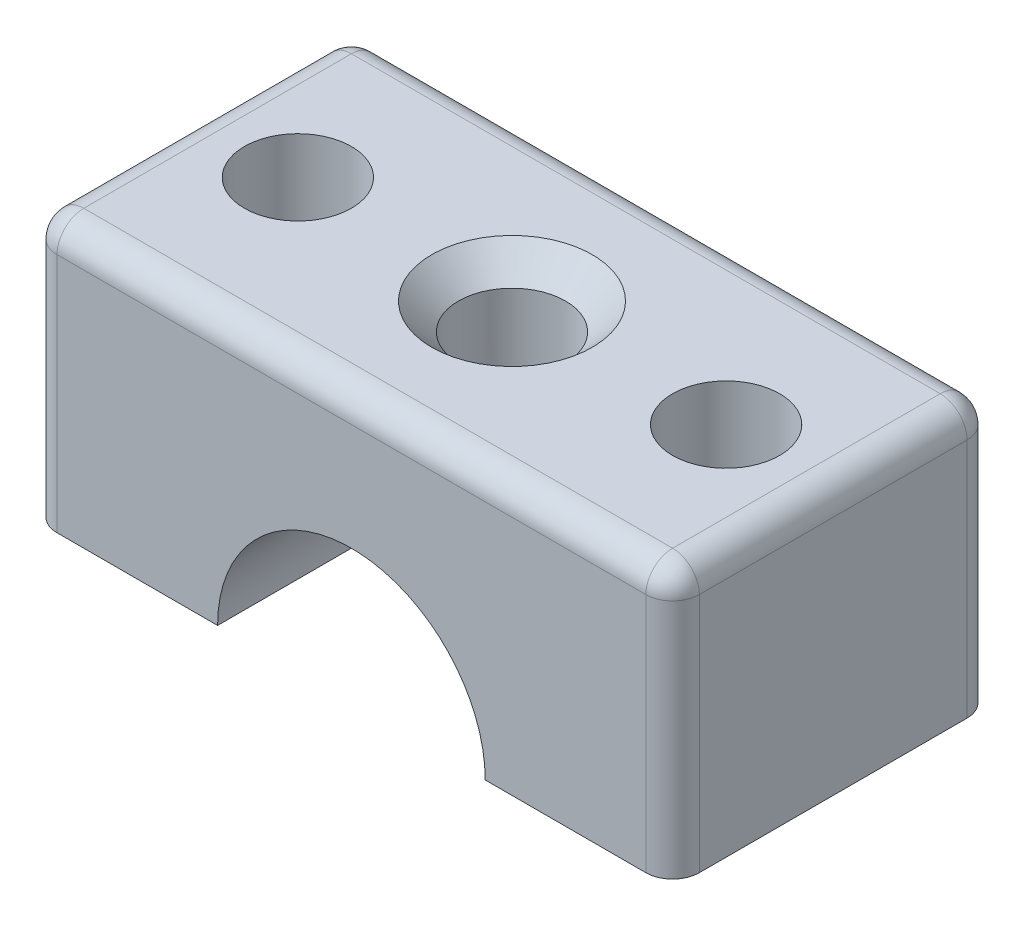
SolidWorks part; units mm, degrees
ref_plane "Front Plane" through (0, 0, 0) normal (0, 0, 1) x (1, 0, 0)
ref_plane "Top Plane" through (0, 0, 0) normal (0, 1, 0) x (1, 0, 0)
ref_plane "Right Plane" through (0, 0, 0) normal (1, 0, 0) x (0, 0, -1)
sketch "Sketch1" plane through (0, 0, 0) normal (0, 1, 0) x (1, 0, 0)
  line L1 (-12, 6) -> (12, 6)
  line L2 (-12, 6) -> (-12, -6)
  line L3 (-12, -6) -> (12, -6)
  line L4 (12, 6) -> (12, -6)
  circle A1 centre (8, 0) radius 2
  circle A2 centre (-8, 0) radius 2
  circle A3 centre (0, 0) radius 2
  point P0 (0, 0)
  point P11 (0, 0)
  dimension "D1" = 24
  dimension "D2" = 12
extrude "Boss-Extrude1" add sketch "Sketch1" along normal blind 10
chamfer "Chamfer1" distance 1 angle 45 1 edges at (0, 10, 2)
fillet "Fillet1" radius 1 8 edges at (-12, 5, -6) (12, 5, -6) (12, 5, 6) (-12, 5, 6) (-12, 10, 0) (0, 10, -6) (12, 10, 0) (0, 10, 6)
sketch "Sketch2" plane through (0, 0, -6) normal (0, 0, -1) x (-1, 0, 0)
  line L0 (-5, 0) -> (5, 0)
  arc A0 (5, 0) -> (-5, 0) centre (0, 0) ccw
extrude "Cut-Extrude1" cut sketch "Sketch2" against normal through all
